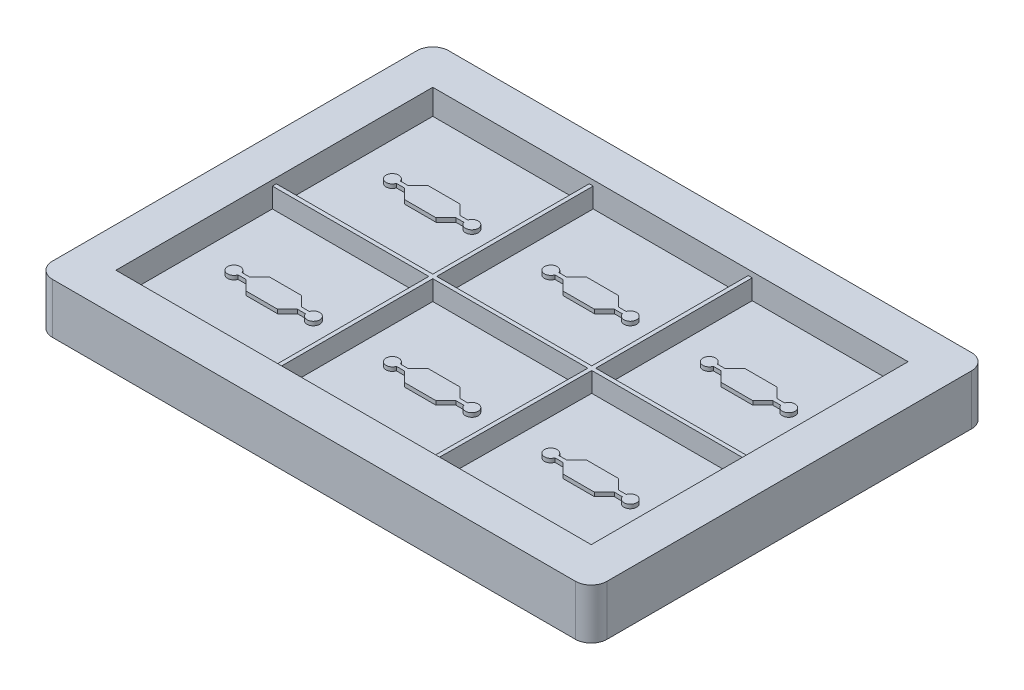
SolidWorks part; units mm, degrees
ref_plane "Front Plane" through (0, 0, 0) normal (0, 0, 1) x (1, 0, 0)
ref_plane "Top Plane" through (0, 0, 0) normal (0, 1, 0) x (1, 0, 0)
ref_plane "Right Plane" through (0, 0, 0) normal (1, 0, 0) x (0, 0, -1)
sketch "Sketch1" plane through (0, 0, 0) normal (0, 1, 0) x (1, 0, 0)
  line L1 (-35, 25) -> (35, 25)
  line L2 (-35, 25) -> (-35, -25)
  line L3 (-35, -25) -> (35, -25)
  line L4 (35, 25) -> (35, -25)
  line L5 (-35, 25) -> (35, -25) construction
  line L6 (-35, -25) -> (35, 25) construction
  point P0 (0, 0)
  dimension "D1" = 70
  dimension "D2" = 50
extrude "Boss-Extrude1" add sketch "Sketch1" along normal blind 6.35
sketch "Sketch2" plane through (0, 6.35, 0) normal (0, 1, 0) x (1, 0, 0)
  line L5 (30, -20) -> (30, 20)
  line L6 (30, -20) -> (30, 20)
  line L11 (30, 20) -> (-30, 20)
  line L12 (-30, 20) -> (-30, -20)
  line L13 (-30, -20) -> (30, -20)
  line L15 (30, 20) -> (-30, 20)
  line L16 (-30, 20) -> (-30, -20)
  line L17 (-30, -20) -> (30, -20)
  dimension "D1" = 5
extrude "Cut-Extrude1" cut sketch "Sketch2" against normal blind 3.175
sketch "Sketch10" plane through (0, 3.175, 0) normal (0, 1, 0) x (1, 0, 0)
  line L0 (-10.25, -0.25) -> (-10.25, -20)
  line L2 (-30, 0.25) -> (-10.25, 0.25)
  line L3 (-30, 0.25) -> (-30, -0.25)
  line L4 (-30, -0.25) -> (-10.25, -0.25)
  line L5 (30, 0.25) -> (30, -0.25)
  line L6 (-30, 0.25) -> (30, -0.25) construction
  line L7 (-30, -0.25) -> (30, 0.25) construction
  line L9 (-10.25, 20) -> (-9.75, 20)
  line L10 (-10.25, 20) -> (-10.25, 0.25)
  line L11 (-10.25, -20) -> (-9.75, -20)
  line L12 (-9.75, 20) -> (-9.75, 0.25)
  line L13 (-10.25, 20) -> (-9.75, -20) construction
  line L14 (-10.25, -20) -> (-9.75, 20) construction
  line L15 (9.8186, 20) -> (10.3186, 20)
  line L16 (9.8186, 20) -> (9.8186, 0.25)
  line L17 (9.6814, -20) -> (10.1814, -20)
  line L18 (10.3186, 20) -> (10.3186, 0.25)
  line L19 (9.8186, 20) -> (10.1814, -20) construction
  line L20 (9.6814, -20) -> (10.3186, 20) construction
  line L22 (-9.75, 0.25) -> (9.8186, 0.25)
  line L24 (-9.75, -0.25) -> (-9.75, -20)
  line L25 (-9.75, -0.25) -> (9.8186, -0.25)
  line L26 (-30, 20) -> (-30, -20) construction
  line L27 (30, -20) -> (30, 20) construction
  line L28 (10.3186, 0.25) -> (30, 0.25)
  line L29 (30, 20) -> (-30, 20) construction
  line L30 (10.3186, -0.25) -> (10.1814, -20)
  line L31 (10.3186, -0.25) -> (30, -0.25)
  line L33 (9.8186, -0.25) -> (9.6814, -20)
  point P0 (0, 0)
  point P1 (0, 0)
  point P6 (-10, 0)
  point P11 (10, 0)
  point P13 (-10, 0)
  point P18 (10, 0)
  dimension "D1" = 20
  dimension "D2" = 20
  dimension "D3" = 0.5
extrude "Dividers" add sketch "Sketch10" along normal blind 2.5
sketch "Sketch11" plane through (0, 3.175, 0) normal (0, 1, 0) x (1, 0, 0)
  line L0 (-24.4649, 10.375) -> (-23.4649, 10.375)
  line L1 (-23.4649, 10.375) -> (-22.2086, 11.6313)
  line L2 (-22.2086, 11.6313) -> (-18.2086, 11.6313)
  line L3 (-18.2086, 11.6313) -> (-16.9524, 10.375)
  line L4 (-16.9524, 10.375) -> (-15.9524, 10.375)
  line L5 (-15.9524, 10.375) -> (-15.9524, 9.875)
  line L6 (-15.9524, 9.875) -> (-16.9524, 9.875)
  line L7 (-16.9524, 9.875) -> (-18.2086, 8.6187)
  line L8 (-18.2086, 8.6187) -> (-22.2086, 8.6187)
  line L9 (-22.2086, 8.6187) -> (-23.4649, 9.875)
  line L10 (-23.4649, 9.875) -> (-24.4649, 9.875)
  line L11 (-24.4649, 9.875) -> (-24.4649, 10.375)
  line L12 (-10.25, 20) -> (-10.25, 0.25) construction
  arc A0 (-24.4649, 10.375) -> (-24.4649, 9.875) centre (-25.2248, 10.125) ccw
  arc A1 (-15.9524, 9.875) -> (-15.9524, 10.375) centre (-15.1924, 10.125) ccw
  point P17 (-10.25, 10.125)
  point P18 (0, 0)
  dimension "D1" = 0.8
  dimension "D2" = 135
  dimension "D3" = 0.5
  dimension "D4" = 4
  dimension "D5" = 1
extrude "Boss-Extrude3" add sketch "Sketch11" along normal blind 0.5 contours L11 A0 | L11 L10 L9 L8 L7 L6 L5 L4 L3 L2 L1 L0 | L5 A1
pattern_linear "LPattern1" count 3 spacing 20 along (1, 0, 0) count 2 spacing 20 along (0, 0, 1) of "Boss-Extrude3"
fillet "Fillet1" radius 2 4 edges at (-35, 3.175, -25) (35, 3.175, -25) (35, 3.175, 25) (-35, 3.175, 25)
equation "\"2.5mmm\"=2"
